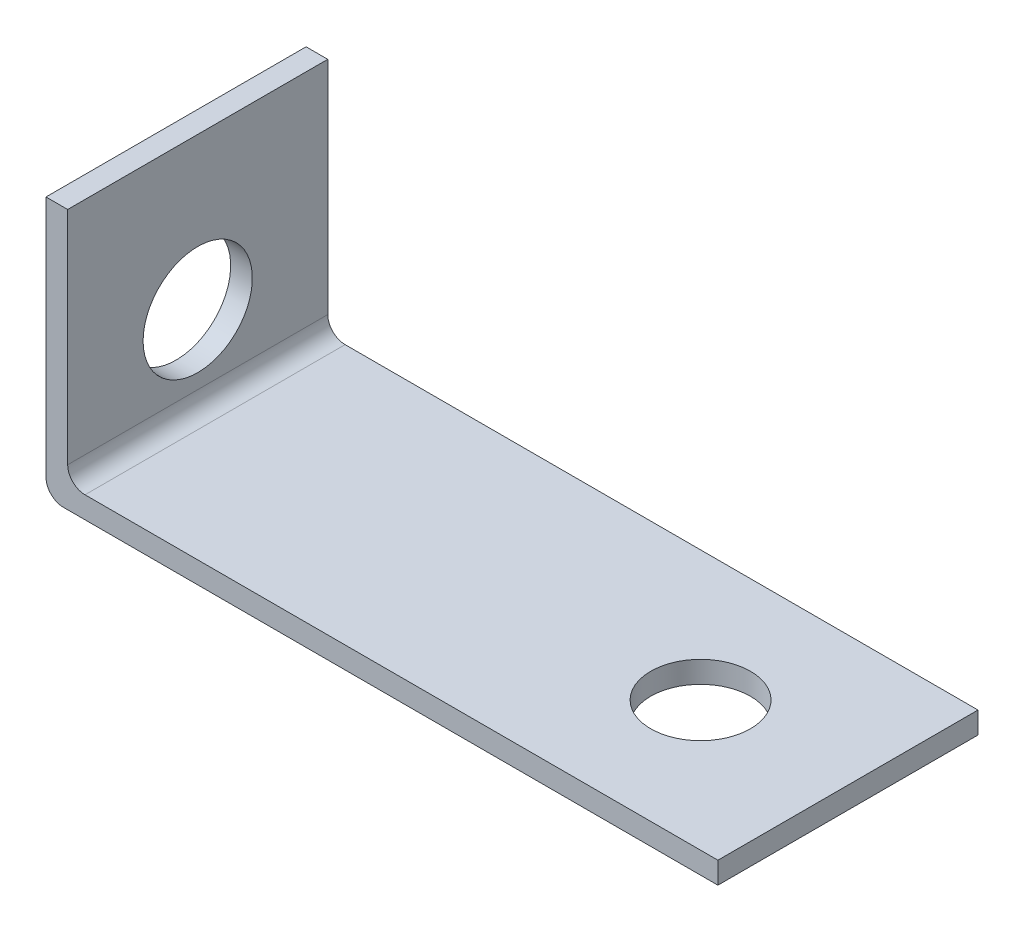
SolidWorks part; units mm, degrees
material "1060 Alloy"
ref_plane "Front Plane" through (0, 0, 0) normal (0, 0, 1) x (1, 0, 0)
ref_plane "Top Plane" through (0, 0, 0) normal (0, 1, 0) x (1, 0, 0)
ref_plane "Right Plane" through (0, 0, 0) normal (1, 0, 0) x (0, 0, -1)
sketch "Sketch1" plane through (0, 0, 0) normal (0, 1, 0) x (1, 0, 0)
  line L1 (-47.625, -19.05) -> (47.625, -19.05)
  line L2 (-47.625, -19.05) -> (-47.625, 19.05)
  line L3 (-47.625, 19.05) -> (47.625, 19.05)
  line L4 (47.625, -19.05) -> (47.625, 19.05)
  line L5 (-47.625, -19.05) -> (47.625, 19.05) construction
  line L6 (-47.625, 19.05) -> (47.625, -19.05) construction
  point P0 (0, 0)
  dimension "D1" = 38.1
  dimension "D2" = 95.25
extrude "Boss-Extrude1" add sketch "Sketch1" along normal blind 3.175
ref_plane "Plane1" through (-47.625, 0, 0) normal (-1, 0, 0) x (0, 0, 1)
sketch "Sketch2" plane through (-47.625, 0, 0) normal (-1, 0, 0) x (0, 0, 1)
  line L1 (-19.05, 0) -> (19.05, 0)
  line L2 (-19.05, 0) -> (-19.05, 38.1)
  line L3 (-19.05, 38.1) -> (19.05, 38.1)
  line L4 (19.05, 0) -> (19.05, 38.1)
  dimension "D1" = 38.1
  dimension "D2" = 38.1
extrude "Boss-Extrude2" add sketch "Sketch2" along normal blind 3.175
sketch "Sketch3" plane through (0, 0, 0) normal (0, 1, 0) x (1, 0, 0)
  line L0 (-47.625, 64.8202) -> (-47.625, -64.8202) construction
  circle A0 centre (26.035, 0) radius 7.3025
  dimension "D2" = 14.605
  dimension "D1" = 73.66
extrude "Cut-Extrude2" cut sketch "Sketch3" along normal through all
sketch "Sketch4" plane through (-47.625, 0, 0) normal (-1, 0, 0) x (0, 0, 1)
  line L0 (-19.05, 0) -> (19.05, 0) construction
  circle A0 centre (0, 15.875) radius 8.001
  dimension "D2" = 16.002
  dimension "D1" = 15.875
extrude "Cut-Extrude3" cut sketch "Sketch4" along normal through all
fillet "Fillet1" radius 2.54 2 edges at (-50.8, 0, 0) (-47.625, 3.175, 0)
